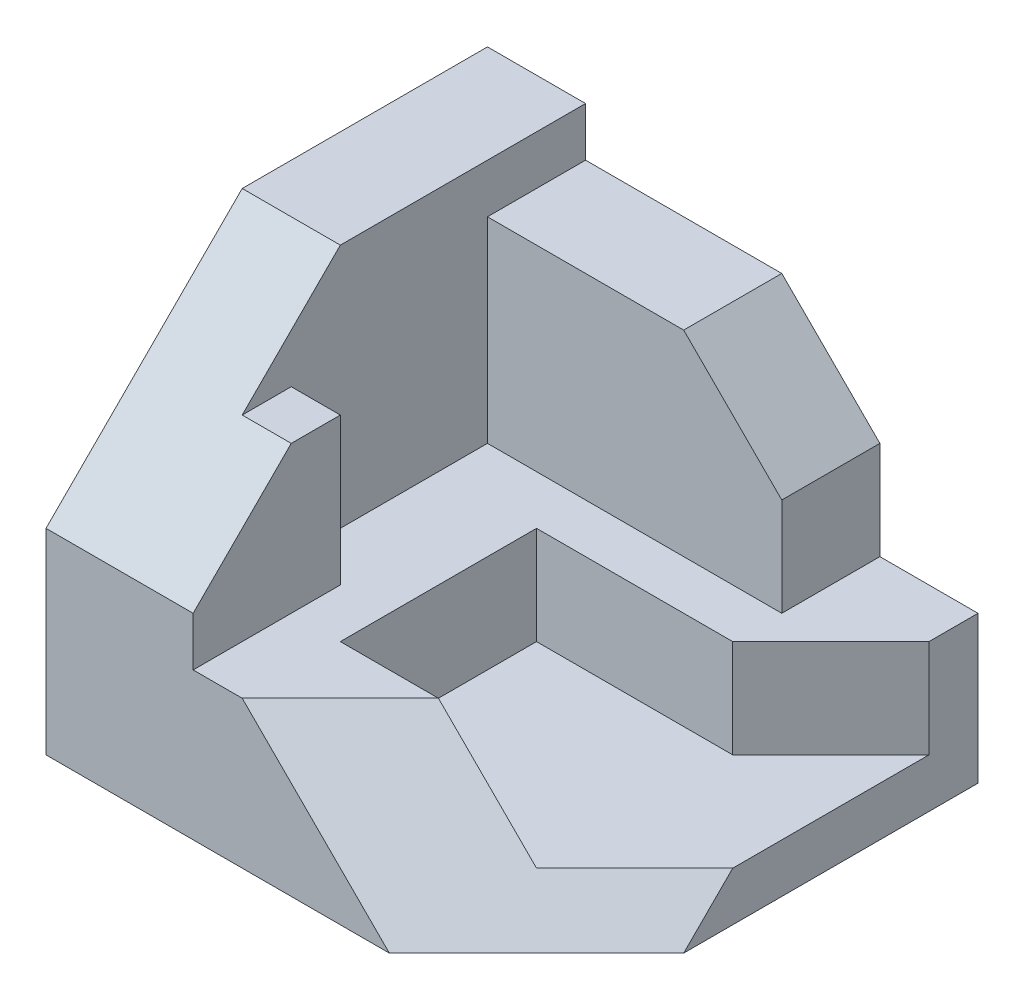
SolidWorks part; units mm, degrees
ref_plane "Front Plane" through (0, 0, 0) normal (0, 0, 1) x (1, 0, 0)
ref_plane "Top Plane" through (0, 0, 0) normal (0, 1, 0) x (1, 0, 0)
ref_plane "Right Plane" through (0, 0, 0) normal (1, 0, 0) x (0, 0, -1)
sketch "Sketch3" plane through (0, 0, 0) normal (0, 0, 1) x (1, 0, 0)
  line L1 (0, 0) -> (100, 0)
  line L2 (0, 0) -> (0, 80)
  line L3 (0, 80) -> (100, 80)
  line L4 (100, 0) -> (100, 80)
  dimension "D1" = 100
  dimension "D2" = 80
extrude "Boss-Extrude1" add sketch "Sketch3" against normal blind 90
sketch "Sketch4" plane through (0, 0, 0) normal (0, 0, 1) x (1, 0, 0)
  line L0 (20, 80) -> (20, 70)
  line L1 (100, 80) -> (0, 80) construction
  line L2 (20, 70) -> (60, 70)
  line L3 (60, 70) -> (80, 50)
  line L4 (80, 50) -> (80, 30)
  line L5 (80, 30) -> (100, 30)
  line L6 (100, 0) -> (100, 80) construction
  line L7 (100, 30) -> (100, 80)
  line L8 (100, 80) -> (20, 80)
  dimension "D1" = 20
  dimension "D2" = 10
  dimension "D3" = 40
  dimension "D4" = 20
  dimension "D5" = 20
  dimension "D6" = 20
extrude "Cut-Extrude1" cut sketch "Sketch4" against normal blind 90
sketch "Sketch5" plane through (0, 0, 0) normal (0, -1, 0) x (-1, 0, 0)
  line L0 (-70, 0) -> (-100, 30)
  line L1 (0, 0) -> (-100, 0) construction
  line L2 (-100, 90) -> (-100, 0) construction
  line L3 (-100, 30) -> (-100, 0)
  line L4 (-100, 0) -> (-70, 0)
  dimension "D1" = 30
  dimension "D2" = 30
extrude "Cut-Extrude2" cut sketch "Sketch5" against normal blind 90
sketch "Sketch7" plane through (0, 0, 0) normal (-1, 0, 0) x (0, 0, 1)
  line L0 (-40, 80) -> (0, 40)
  line L1 (-90, 80) -> (0, 80) construction
  line L2 (0, 80) -> (0, 0) construction
  line L3 (0, 40) -> (0, 80)
  line L4 (0, 80) -> (-40, 80)
  dimension "D1" = 40
  dimension "D2" = 40
extrude "Cut-Extrude3" cut sketch "Sketch7" against normal blind 90
sketch "Sketch8" plane through (0, 70, 0) normal (0, 1, 0) x (1, 0, 0)
  line L1 (60, 90) -> (20, 90)
  line L2 (60, 90) -> (60, 30)
  line L3 (60, 30) -> (20, 30)
  line L4 (20, 90) -> (20, 30)
extrude "Cut-Extrude4" cut sketch "Sketch8" against normal blind 60
sketch "Sketch9" plane through (0, 0, -30) normal (0, 0, -1) x (-1, 0, 0)
  line L1 (-60, 70) -> (-30, 70)
  line L2 (-60, 70) -> (-60, 40)
  line L3 (-60, 40) -> (-30, 40)
  line L4 (-30, 70) -> (-30, 40)
  line L5 (-70, 40) -> (0, 40) construction
  dimension "D1" = 10
  dimension "D2" = 30
extrude "Cut-Extrude5" cut sketch "Sketch9" against normal blind 60
sketch "Sketch10" plane through (0, 0, -30) normal (0, 0, -1) x (-1, 0, 0)
  line L0 (-30, 40) -> (-30, 70) construction
  line L1 (-20, 70) -> (-30, 70)
  line L2 (-20, 70) -> (-20, 60)
  line L3 (-20, 60) -> (-30, 60)
  line L4 (-30, 70) -> (-30, 60)
  dimension "D1" = 10
extrude "Cut-Extrude6" cut sketch "Sketch10" against normal blind 60
sketch "Sketch11" plane through (0, 10, 0) normal (0, 1, 0) x (1, 0, 0)
  line L1 (20, 90) -> (60, 90)
  line L2 (20, 90) -> (20, 30)
  line L3 (20, 30) -> (60, 30)
  line L4 (60, 90) -> (60, 30)
extrude "Boss-Extrude2" add sketch "Sketch11" along normal blind 20
sketch "Sketch12" plane through (0, 30, 0) normal (0, 1, 0) x (1, 0, 0)
  line L0 (60, 30) -> (60, 90) construction
  line L1 (20, 90) -> (60, 90)
  line L2 (20, 90) -> (20, 70)
  line L3 (20, 70) -> (60, 70)
  line L4 (60, 90) -> (60, 70)
  dimension "D1" = 20
extrude "Boss-Extrude3" add sketch "Sketch12" along normal blind 40
sketch "Sketch13" plane through (0, 0, -30) normal (0, 0, -1) x (-1, 0, 0)
  line L0 (-20, 30) -> (-60, 30) construction
  line L1 (-30, 40) -> (-60, 40)
  line L2 (-30, 40) -> (-30, 30)
  line L3 (-30, 30) -> (-60, 30)
  line L4 (-60, 40) -> (-60, 30)
extrude "Cut-Extrude7" cut sketch "Sketch13" against normal blind 40
sketch "Sketch15" plane through (60, 0, 0) normal (-1, 0, 0) x (0, 0, 1)
  line L0 (-70, 70) -> (-70, 30)
  line L1 (-70, 30) -> (0, 30)
  line L2 (0, 30) -> (0, 40)
  line L3 (0, 40) -> (-30, 70)
  line L4 (-30, 70) -> (-70, 70)
extrude "Cut-Extrude8" cut sketch "Sketch15" against normal blind 40
sketch "Sketch16" plane through (0, 30, 0) normal (0, 1, 0) x (1, 0, 0)
  line L0 (100, 80) -> (80, 60)
  line L1 (100, 90) -> (100, 30) construction
  line L2 (80, 60) -> (40, 60)
  line L3 (40, 60) -> (40, 20)
  line L4 (40, 20) -> (80, 20)
  line L5 (80, 20) -> (100, 40)
  line L6 (100, 80) -> (100, 40)
  dimension "D1" = 10
  dimension "D2" = 20
  dimension "D3" = 20
  dimension "D4" = 40
  dimension "D5" = 40
  dimension "D6" = 40
  dimension "D7" = 20
extrude "Cut-Extrude9" cut sketch "Sketch16" against normal blind 20
ref_plane "Plane3" through (0, 0, -50) normal (0, 0, 1) x (1, 0, 0)
sketch "Sketch17" plane through (0, 0, -50) normal (0, 0, 1) x (1, 0, 0)
  line L1 (100, 10) -> (80, 10)
  line L2 (100, 10) -> (100, 30)
  line L3 (100, 30) -> (80, 30)
  line L4 (80, 10) -> (80, 30)
  dimension "D1" = 20
  dimension "D2" = 20
  dimension "D3" = 0
  dimension "D4" = 0
extrude "Cut-Extrude10" cut sketch "Sketch17" along normal blind 84
ref_plane "Plane4" through (0, 0, -10) normal (0, 0, 1) x (1, 0, 0)
sketch "Sketch19" plane through (0, 0, -10) normal (0, 0, 1) x (1, 0, 0)
  line L0 (80, 10) -> (60, 30)
  line L1 (60, 30) -> (80, 30)
  line L2 (80, 30) -> (80, 10)
  dimension "D1" = 20
extrude "Cut-Extrude12" cut sketch "Sketch19" along normal blind 20
sketch "Sketch22" plane through (0, 0, -10) normal (0, 0, 1) x (1, 0, 0)
  line L0 (60, 30) -> (80, 30)
  line L1 (80, 30) -> (80, 10)
  line L2 (80, 10) -> (60, 30)
extrude "Cut-Extrude15" cut sketch "Sketch22" against normal blind 10
sketch "Sketch23" plane through (0, 0, 0) normal (0, 0, 1) x (1, 0, 0)
  line L0 (40, 30) -> (70, 0)
  line L1 (60, 30) -> (30, 30) construction
  line L2 (0, 0) -> (70, 0) construction
  dimension "D1" = 70
  dimension "D2" = 30
ref_plane "Plane5" through (23.3333, 23.3333, 23.3333) normal (0.5774, 0.5774, 0.5774) x (0.4082, 0.4082, -0.8165)
sketch "Sketch24" plane through (23.3333, 23.3333, 23.3333) normal (0.5774, 0.5774, 0.5774) x (0.4082, 0.4082, -0.8165)
  line L0 (53.0723, -21.2132) -> (28.5774, -7.0711)
  line L1 (28.5774, -7.0711) -> (28.5774, -49.4975)
  line L2 (28.5774, -49.4975) -> (53.0723, -49.4975)
  line L3 (53.0723, -49.4975) -> (53.0723, -21.2132)
extrude "Cut-Extrude17" cut sketch "Sketch24" along normal blind 77
ref_plane "Plane6" through (5, 15, 10) normal (0.2673, 0.8018, 0.5345) x (0.9636, -0.2224, -0.1482)
sketch "Sketch26" plane through (35, -35, 0) normal (-0.7071, 0.7071, 0) x (0, 0, 1)
  line L0 (-20, 63.6396) -> (-10, 63.6396)
  line L1 (-10, 63.6396) -> (0, 49.4975)
  line L2 (0, 49.4975) -> (-20, 63.6396)
extrude "Cut-Extrude19" cut sketch "Sketch26" against normal blind 77
sketch "Sketch27" plane through (45, 45, 0) normal (-0.7071, -0.7071, 0) x (0, 0, 1)
  line L0 (-20, -49.4975) -> (-10, -49.4975)
  line L1 (-10, -49.4975) -> (-20, -63.6396)
  line L2 (-20, -63.6396) -> (-20, -49.4975)
extrude "Cut-Extrude20" cut sketch "Sketch27" against normal blind 77
sketch "Sketch29" plane through (0, 10, 0) normal (0, 1, 0) x (1, 0, 0)
  line L0 (80, 20) -> (100, 40)
  line L1 (100, 30) -> (100, 80) construction
  line L2 (90, 20) -> (100, 30) construction
ref_plane "Plane7" through (23.3333, 23.3333, 23.3333) normal (-0.5774, -0.5774, -0.5774) x (-0.8165, 0.4082, 0.4082)
sketch "Sketch30" plane through (23.3333, 23.3333, 23.3333) normal (-0.5774, -0.5774, -0.5774) x (-0.8165, 0.4082, 0.4082)
  line L0 (-69.4022, 21.2132) -> (-93.8971, 35.3553)
  line L1 (-93.8971, 35.3553) -> (-93.8971, 21.2132)
  line L2 (-69.4022, 21.2132) -> (-81.6497, 14.1421)
  line L3 (-81.6497, 14.1421) -> (-93.8971, 21.2132)
extrude "Cut-Extrude21" cut sketch "Sketch30" against normal blind 77
